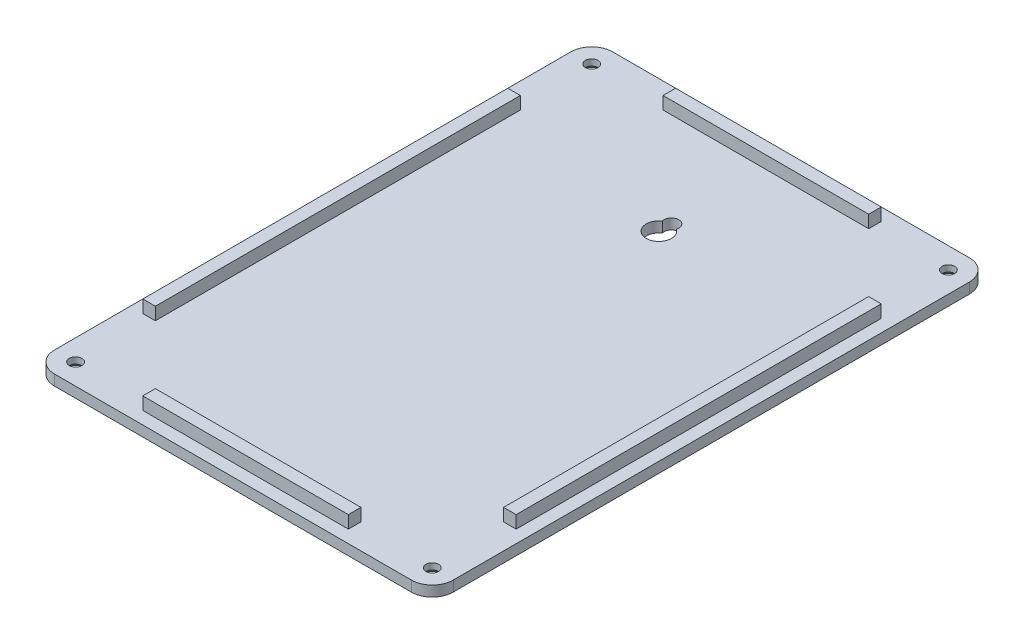
SolidWorks part; units mm, degrees
ref_plane "Спереди" through (0, 0, 0) normal (0, 0, 1) x (1, 0, 0)
ref_plane "Сверху" through (0, 0, 0) normal (0, 1, 0) x (1, 0, 0)
ref_plane "Справа" through (0, 0, 0) normal (1, 0, 0) x (0, 0, -1)
sketch "Эскиз1" plane through (0, 0, 0) normal (0, 1, 0) x (1, 0, 0)
  line L0 (-1000, 0) -> (49000, 0) construction
  line L1 (0, -1000) -> (0, 49000) construction
  line L2 (47.5, -1000) -> (47.5, 49000) construction
  line L3 (-47.5, -1000) -> (-47.5, 49000) construction
  line L4 (-1000, -66.5) -> (49000, -66.5) construction
  line L5 (-1000, 66.5) -> (49000, 66.5) construction
  line L6 (-42.5, -66.5) -> (42.5, -66.5)
  line L7 (47.5, -61.5) -> (47.5, 61.5)
  line L8 (42.5, 66.5) -> (-42.5, 66.5)
  line L9 (-47.5, 61.5) -> (-47.5, -61.5)
  arc A0 (-42.5, -66.5) -> (-47.5, -61.5) centre (-42.5, -61.5) cw
  arc A1 (42.5, -66.5) -> (47.5, -61.5) centre (42.5, -61.5) ccw
  arc A2 (47.5, 61.5) -> (42.5, 66.5) centre (42.5, 61.5) ccw
  arc A3 (-42.5, 66.5) -> (-47.5, 61.5) centre (-42.5, 61.5) ccw
  point P19 (-47.5, -66.5)
  point P22 (47.5, -66.5)
  point P25 (47.5, 66.5)
  point P28 (-47.5, 66.5)
  dimension "D1" = 5
extrude "Бобышка-Вытянуть1" add sketch "Эскиз1" along normal blind 2.5
sketch "Эскиз2" plane through (0, 2.5, 0) normal (0, 1, 0) x (1, 0, 0)
  line L0 (-1019.3742, -66.5) -> (48980.6258, -66.5) construction
  line L2 (-1024.6252, 66.5) -> (48975.3748, 66.5) construction
  line L4 (-47.5, -988.8644) -> (-47.5, 49011.1356) construction
  line L6 (47.5, -985.7862) -> (47.5, 49014.2138) construction
  line L8 (42.5, -985.7862) -> (42.5, 49014.2138) construction
  line L9 (-42.5, -988.8644) -> (-42.5, 49011.1356) construction
  line L10 (-1024.6252, 61.5) -> (48975.3748, 61.5) construction
  line L11 (-1019.3742, -61.5) -> (48980.6258, -61.5) construction
  circle A0 centre (-42.5, 61.5) radius 1.5
  circle A1 centre (42.5, 61.5) radius 1.5
  circle A2 centre (42.5, -61.5) radius 1.5
  circle A3 centre (-42.5, -61.5) radius 1.5
  dimension "D1" = 5
  dimension "D2" = 5
  dimension "D3" = 5
  dimension "D4" = 5
extrude "Вырез-Вытянуть1" cut sketch "Эскиз2" against normal blind 11
sketch "Эскиз3" plane through (0, 2.5, 0) normal (0, 1, 0) x (1, 0, 0)
  line L0 (-1032.4111, 66.5) -> (48967.5889, 66.5) construction
  line L2 (-1015.9339, -66.5) -> (48984.0661, -66.5) construction
  line L4 (-47.5, -977.8192) -> (-47.5, 49022.1808) construction
  line L6 (47.5, -985.7862) -> (47.5, 49014.2138) construction
  line L8 (44.5, -985.7862) -> (44.5, 49014.2138) construction
  line L9 (-1032.4111, 63.5) -> (48967.5889, 63.5) construction
  line L10 (-44.5, -977.8192) -> (-44.5, 49022.1808) construction
  line L11 (-1015.9339, -63.5) -> (48984.0661, -63.5) construction
  line L12 (-1032.4111, 43.5) -> (48967.5889, 43.5) construction
  line L13 (-1015.9339, -43.5) -> (48984.0661, -43.5) construction
  line L14 (-24.5, -977.8192) -> (-24.5, 49022.1808) construction
  line L15 (24.5, -985.7862) -> (24.5, 49014.2138) construction
  line L16 (-24.5, 63.5) -> (24.5, 63.5)
  line L17 (-24.5, -63.5) -> (24.5, -63.5)
  line L18 (-44.5, 43.5) -> (-44.5, -43.5)
  line L19 (44.5, 43.5) -> (44.5, -43.5)
  line L20 (-24.5, 60.5) -> (24.5, 60.5)
  line L21 (-41.5, 43.5) -> (-41.5, -43.5)
  line L22 (41.5, 43.5) -> (41.5, -43.5)
  line L23 (-24.5, -60.5) -> (24.5, -60.5)
  line L24 (-24.5, 63.5) -> (-24.5, 60.5)
  line L25 (24.5, 60.5) -> (24.5, 63.5)
  line L26 (41.5, 43.5) -> (44.5, 43.5)
  line L27 (-44.5, 43.5) -> (-41.5, 43.5)
  line L28 (-44.5, -43.5) -> (-41.5, -43.5)
  line L29 (41.5, -43.5) -> (44.5, -43.5)
  line L30 (24.5, -63.5) -> (24.5, -60.5)
  line L31 (-24.5, -63.5) -> (-24.5, -60.5)
  dimension "D1" = 3
  dimension "D2" = 3
  dimension "D3" = 3
  dimension "D4" = 3
  dimension "D5" = 20
  dimension "D6" = 20
  dimension "D7" = 20
  dimension "D8" = 20
  dimension "D9" = 3
  dimension "D10" = 3
  dimension "D11" = 3
  dimension "D12" = 3
extrude "Бобышка-Вытянуть2" add sketch "Эскиз3" along normal blind 3
sketch "Эскиз4" plane through (0, 2.5, 0) normal (0, 1, 0) x (1, 0, 0)
  line L0 (0, -1000) -> (0, 49000) construction
  line L1 (-1000, 0) -> (49000, 0) construction
  line L2 (-1000, 35) -> (49000, 35) construction
  circle A0 centre (0, 35) radius 3 construction
  circle A1 centre (0, 38) radius 1.75 construction
  arc A2 (-1.6739, 37.4896) -> (1.6739, 37.4896) centre (0, 38) cw
  arc A3 (-1.6739, 37.4896) -> (1.6739, 37.4896) centre (0, 35) ccw
extrude "Вырез-Вытянуть2" cut sketch "Эскиз4" against normal blind 6
chamfer "Фаска1" distance 1 angle 45 4 edges at (42.5, 0, 60) (-42.5, 0, -63) (42.5, 0, -63) (-42.5, 0, 60)
